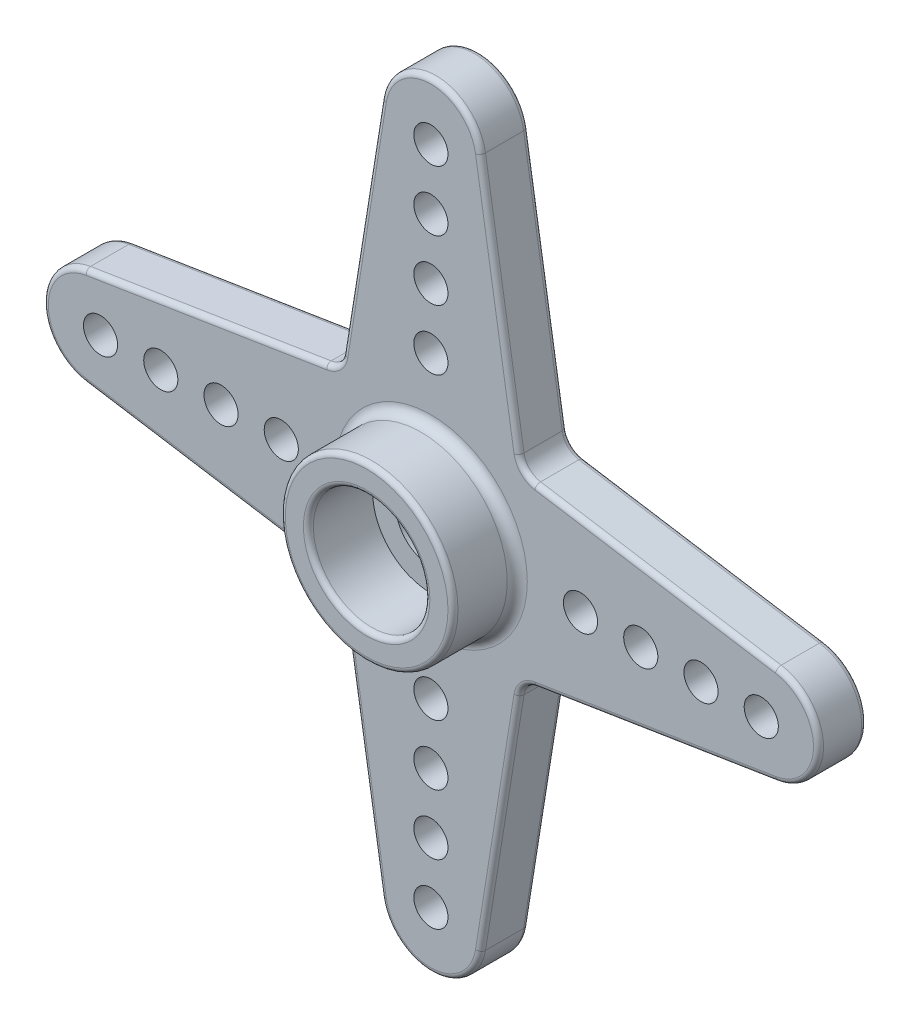
SolidWorks part; units mm, degrees
ref_plane "Front Plane" through (0, 0, 0) normal (0, 0, 1) x (1, 0, 0)
ref_plane "Top Plane" through (0, 0, 0) normal (0, 1, 0) x (1, 0, 0)
ref_plane "Right Plane" through (0, 0, 0) normal (1, 0, 0) x (0, 0, -1)
sketch "Sketch1" plane through (0, 0, 0) normal (0, 0, 1) x (1, 0, 0)
  line L0 (-4.5, 4.5) -> (-17.195, 2.4686)
  line L1 (-17.195, -2.4686) -> (-4.5, -4.5)
  line L2 (0, 16.8) -> (0, -16.8) construction
  line L3 (16.8, 0) -> (-16.8, 0) construction
  line L4 (17.195, -2.4686) -> (4.5, -4.5)
  line L5 (4.5, 4.5) -> (17.195, 2.4686)
  line L6 (4.5, 4.5) -> (2.4686, 17.195)
  line L7 (-2.4686, 17.195) -> (-4.5, 4.5)
  line L8 (-2.4686, -17.195) -> (-4.5, -4.5)
  line L9 (4.5, -4.5) -> (2.4686, -17.195)
  line L10 (4.5, 4.5) -> (4.5, -4.5) construction
  line L11 (4.5, 4.5) -> (-4.5, 4.5) construction
  arc A0 (2.4686, -17.195) -> (-2.4686, -17.195) centre (0, -16.8) cw
  circle A1 centre (0, 0) radius 1.75
  arc A2 (-17.195, 2.4686) -> (-17.195, -2.4686) centre (-16.8, 0) ccw
  arc A3 (17.195, 2.4686) -> (17.195, -2.4686) centre (16.8, 0) cw
  arc A5 (2.4686, 17.195) -> (-2.4686, 17.195) centre (0, 16.8) ccw
  point P10 (-2.4801, 14.0164)
  point P17 (0, 0)
  dimension "D1" = 33.6
  dimension "D2" = 3.5
  dimension "D3" = 2.5
  dimension "D4" = 9
extrude "Boss-Extrude1" add sketch "Sketch1" along normal blind 2.4
sketch "Sketch2" plane through (0, 0, 2.4) normal (0, 0, 1) x (1, 0, 0)
  circle A0 centre (0, 0) radius 4.3
  circle A1 centre (0, 0) radius 2.9
  point P4 (0.4797, -0.8335)
  dimension "D1" = 8.6
  dimension "D2" = 5.8
extrude "Boss-Extrude2" add sketch "Sketch2" along normal blind 3.2
sketch "Sketch4" plane through (0, 0, 0) normal (0, 0, -1) x (-1, 0, 0)
  circle A0 centre (0, 0) radius 3.3
  circle A1 centre (0, 0) radius 3.6
  dimension "D1" = 7.2
  dimension "D2" = 6.6
extrude "Boss-Extrude3" add sketch "Sketch4" along normal blind 0.2
sketch "Sketch5" plane through (0, 0, 0) normal (0, 0, -1) x (-1, 0, 0)
  circle A0 centre (0, 0) radius 3.3 construction
  circle A1 centre (0, 0) radius 3.3
  circle A2 centre (0, 0) radius 4
  circle A3 centre (0, 0) radius 3.6 construction
  circle A4 centre (0, 0) radius 3.6
  dimension "D1" = 8
extrude "Cut-Extrude2" cut sketch "Sketch5" against normal blind 0.4
sketch "Sketch6" plane through (0, 0, 0) normal (0, 0, -1) x (-1, 0, 0)
  line L0 (0, 0) -> (0, 1.0197) construction
  circle A1 centre (7.45, 0) radius 0.85
  dimension "D1" = 1.7
  dimension "D2" = 7.45
extrude "Cut-Extrude3" cut sketch "Sketch6" against normal through all
pattern_linear "LPattern1" count 4 spacing 3 along (-1, 0, 0) of "Cut-Extrude3"
pattern_circular "CirPattern1" count 4 over 360 about axis through (0, 0, 0) along (0, 0, 1) of "Cut-Extrude3", "LPattern1"
fillet "Fillet3" radius 1 4 edges at (-4.5, -4.5, 1.2) (4.5, -4.5, 1.2) (4.5, 4.5, 1.2) (-4.5, 4.5, 1.2)
fillet "Fillet1" radius 0.25 34 edges at (4.3, 0, 5.6) (2.9, 0, 5.6) (-11.205, -3.4271, 2.4) (-19.3, 0, 2.4) (-11.205, 3.4271, 2.4) (11.205, 3.4271, 2.4) (19.3, 0, 2.4) (11.205, -3.4271, 2.4) (-11.205, -3.4271, 0) (-19.3, 0, 0) (-11.205, 3.4271, 0) (11.205, 3.4271, 0) (19.3, 0, 0) (11.205, -3.4271, 0) (-4.6659, 4.6659, 2.4) (-3.4271, 11.205, 2.4) (0, 19.3, 2.4) (3.4271, 11.205, 2.4) (4.6659, 4.6659, 2.4) (4.6659, -4.6659, 2.4) (3.4271, -11.205, 2.4) (0, -19.3, 2.4) (-3.4271, -11.205, 2.4) (-4.6659, -4.6659, 2.4) (-4.6659, 4.6659, 0) (-3.4271, 11.205, 0) (0, 19.3, 0) (3.4271, 11.205, 0) (4.6659, 4.6659, 0) (4.6659, -4.6659, 0) (3.4271, -11.205, 0) (0, -19.3, 0) (-3.4271, -11.205, 0) (-4.6659, -4.6659, 0)
fillet "Fillet2" radius 0.5 1 edges at (4.3, 0, 2.4)
